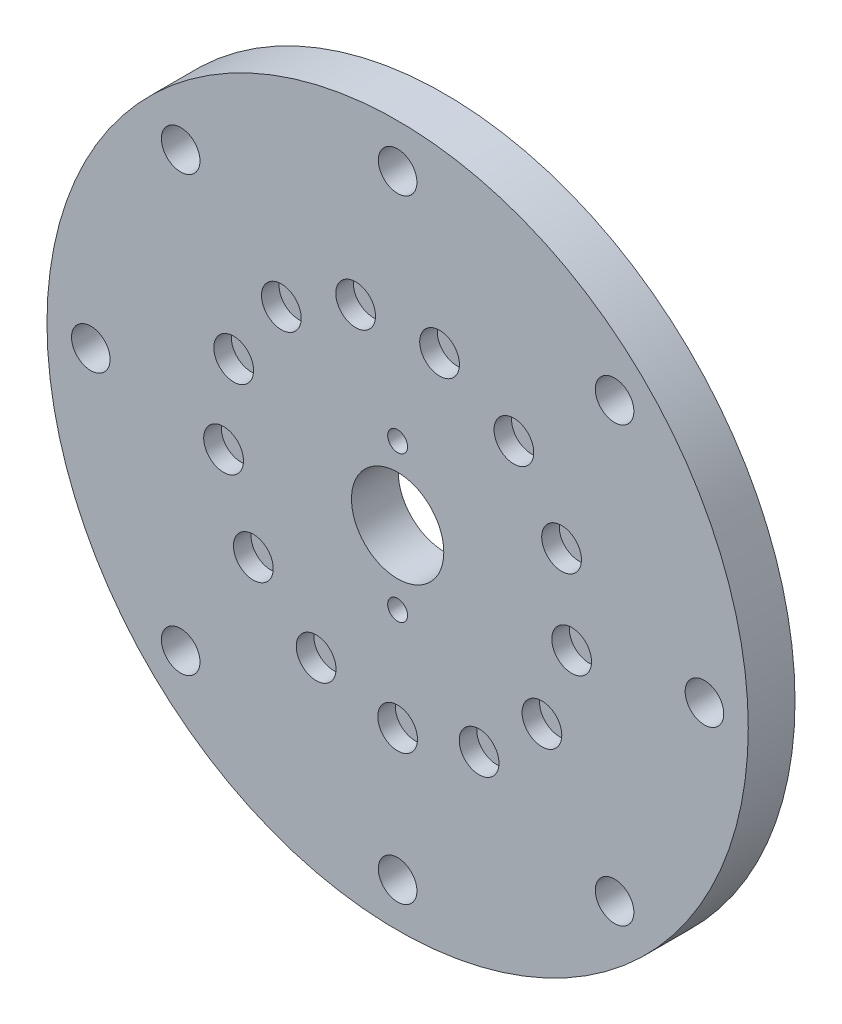
SolidWorks part; units mm, degrees
ref_plane "Front Plane" through (0, 0, 0) normal (0, 0, 1) x (1, 0, 0)
ref_plane "Top Plane" through (0, 0, 0) normal (0, 1, 0) x (1, 0, 0)
ref_plane "Right Plane" through (0, 0, 0) normal (1, 0, 0) x (0, 0, -1)
sketch "Sketch1" plane through (0, 0, 0) normal (0, 0, 1) x (1, 0, 0)
  circle A0 centre (0, 0) radius 60
  circle A1 centre (0, 0) radius 7.9
  dimension "D1" = 120
  dimension "D2" = 15.8
extrude "Boss-Extrude1" add sketch "Sketch1" along normal blind 8
sketch "Sketch2" plane through (0, 0, 8) normal (0, 0, 1) x (1, 0, 0)
  circle A0 centre (0, 12.5) radius 1.7
  circle A1 centre (0, 0) radius 12.5 construction
  circle A2 centre (0, -12.5) radius 1.7
  point P10 (0, 0)
  dimension "D1" = 3.4
  dimension "D2" = 25
  dimension "D3" = 2
extrude "Cut-Extrude1" cut sketch "Sketch2" against normal through all
sketch "Sketch3" plane through (0, 0, 8) normal (0, 0, 1) x (1, 0, 0)
  line L0 (0, 0) -> (29.997, -0.4234) construction
  line L1 (0, 0) -> (29.7813, -3.6159) construction
  circle A0 centre (0, 0) radius 30 construction
  circle A1 centre (29.7813, -3.6159) radius 3.4
  circle A2 centre (24.6897, -17.0417) radius 3.4
  circle A3 centre (13.9419, -26.5636) radius 3.4
  circle A4 centre (0.0002, -30) radius 3.4
  circle A5 centre (-13.9415, -26.5638) radius 3.4
  circle A6 centre (-24.6894, -17.0421) radius 3.4
  circle A7 centre (-29.7812, -3.6163) radius 3.4
  circle A8 centre (-28.0506, 10.6379) radius 3.4
  circle A9 centre (-19.8939, 22.4552) radius 3.4
  circle A10 centre (-7.1797, 29.1282) radius 3.4
  circle A11 centre (7.1792, 29.1283) radius 3.4
  circle A12 centre (19.8935, 22.4555) radius 3.4
  circle A13 centre (28.0504, 10.6384) radius 3.4
  circle A14 centre (0, 12.5) radius 1.7 construction
  point P32 (0, 0)
  dimension "D1" = 60
  dimension "D2" = 6.8
  dimension "D4" = 6.114
  dimension "D5" = 0.0002
  dimension "D3" = 13
extrude "Cut-Extrude2" cut sketch "Sketch3" against normal blind 3
sketch "Sketch6" plane through (0, 0, 8) normal (0, 0, 1) x (1, 0, 0)
  circle A0 centre (0, 0) radius 52.5
  circle A1 centre (0, 0) radius 60 construction
  point P6 (0, 52.5)
  point P15 (37.1231, 37.1231)
  point P16 (52.5, 0)
  point P17 (37.1231, -37.1231)
  point P18 (0, -52.5)
  point P19 (-37.1231, -37.1231)
  point P20 (-52.5, 0)
  point P21 (-37.1231, 37.1231)
  dimension "D1" = 7.5
  dimension "D2" = 8
hole_wizard "M6 Clearance Hole1" positions "Sketch6" profile "Sketch5" hole size "M6" standard "ISO" end condition through all
sketch "Sketch5" plane through (-37.1231, 37.1231, 8) normal (1, 0, 0) x (0, -1, 0)
  line L0 (0, 0) -> (0, 8)
  line L1 (0, 8) -> (3.3, 8)
  line L2 (3.3, 8) -> (3.3, 0)
  line L5 (3.3, 0) -> (0, 0)
  line L11 (0, -6.35) -> (0, 107.95) construction
  dimension "Thru Hole Dia." = 6.6
  dimension "Thru Hole Depth" = 8
